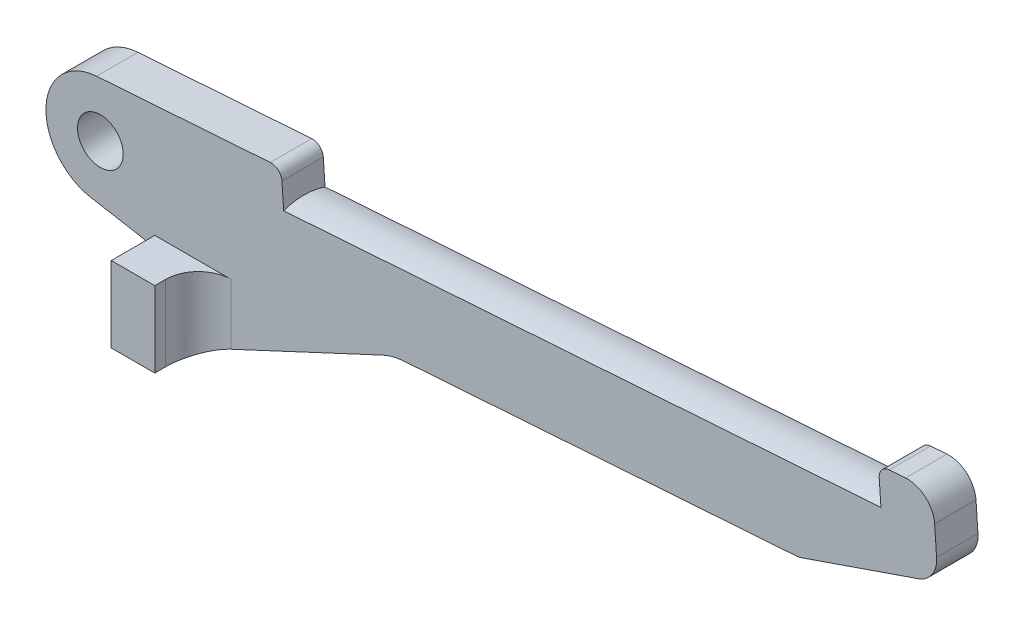
SolidWorks part; units mm, degrees
ref_plane "Front Plane" through (0, 0, 0) normal (0, 0, 1) x (1, 0, 0)
ref_plane "Top Plane" through (0, 0, 0) normal (0, 1, 0) x (1, 0, 0)
ref_plane "Right Plane" through (0, 0, 0) normal (1, 0, 0) x (0, 0, -1)
sketch "Sketch1" plane through (0, 0, 0) normal (0, 0, 1) x (1, 0, 0)
  line L0 (10, 131.0662) -> (10, -29.5109) construction
  line L1 (-1.7365, -9.8481) -> (7.5209, -11.4804)
  line L2 (10, -14.4348) -> (10, -23.9175)
  line L3 (10, -23.9175) -> (18, -23.9175)
  line L4 (18, -23.9175) -> (52.0166, -8.0553)
  line L5 (55.5452, -7.1428) -> (127.6748, -2.099)
  line L6 (88.2212, -3) -> (186.7715, -3) construction
  line L7 (184.3331, 3) -> (92.8947, 3) construction
  line L8 (153.6363, 10.5795) -> (153.2761, 15.7303)
  line L9 (-0.6976, 9.9756) -> (33.2196, 12.3474)
  line L10 (33.2196, 12.3474) -> (33.6382, 6.362)
  line L11 (33.6382, 6.362) -> (143.3702, 14.0352)
  line L12 (143.3702, 14.0352) -> (142.9517, 20.0206)
  line L13 (142.9517, 20.0206) -> (147.9395, 20.3694)
  line L14 (33.6382, 6.362) -> (25.6162, 121.0818) construction
  line L15 (25.6162, 121.0818) -> (25.2572, 121.0567) construction
  line L16 (150.2763, 5.5032) -> (128.9539, -1.8387)
  circle A0 centre (0, 0) radius 4.2
  arc A1 (-0.6976, 9.9756) -> (-1.7365, -9.8481) centre (0, 0) ccw
  arc A2 (127.6748, -2.099) -> (128.9539, -1.8387) centre (127.326, 2.8889) ccw
  arc A3 (147.9395, 20.3694) -> (153.2761, 15.7303) centre (148.2883, 15.3815) cw
  arc A4 (7.5209, -11.4804) -> (10, -14.4348) centre (7, -14.4348) cw
  arc A5 (52.0166, -8.0553) -> (55.5452, -7.1428) centre (56.2428, -17.1184) cw
  arc A6 (153.6363, 10.5795) -> (150.2763, 5.5032) centre (148.6484, 10.2307) cw
  point P24 (152.9273, 20.7181)
  point P32 (10, -11.9175)
  point P36 (153.9039, 6.7522)
  dimension "D1" = 8.4
  dimension "D3" = 20
  dimension "D17" = 8
  dimension "D18" = 15
  dimension "D19" = 3
  dimension "D20" = 10
  dimension "D21" = 5
  dimension "D13" = 5
  dimension "D2" = 10
  dimension "D4" = 280
  dimension "D5" = 8
  dimension "D6" = 12
  dimension "D7" = 86
  dimension "D8" = 34
  dimension "D9" = 6
  dimension "D10" = 110
  dimension "D11" = 10
  dimension "D12" = 15
  dimension "D14" = 25
  dimension "D15" = 6
  dimension "D16" = 115
extrude "Boss-Extrude1" add sketch "Sketch1" along normal blind 7.6
sketch "Sketch2" plane through (0, 0, 7.6) normal (0, 0, 1) x (1, 0, 0)
  line L1 (10, -23.9175) -> (18, -23.9175)
  line L2 (10, -23.9175) -> (10, -10)
  line L3 (10, -10) -> (18, -10)
  line L4 (18, -23.9175) -> (18, -10)
  dimension "D1" = 10
extrude "Boss-Extrude2" add sketch "Sketch2" along normal blind 8
fillet "Fillet1" radius 6 1 edges at (18, -16.9588, 7.6)
sketch "Sketch6" plane through (22.5121, 165.472, 0) normal (-0.9976, -0.0698, 0) x (0, 0, -1)
  line L1 (-7.6, 159.4986) -> (-7.6, 153.4986) construction
  line L2 (-7.6, 153.4986) -> (0, 153.4986) construction
  line L3 (0, 159.4986) -> (0, 153.4986) construction
  line L4 (-7.6, 160.1161) -> (-7.6, 153.4986)
  line L5 (-7.6, 153.4986) -> (0, 153.4986)
  line L10 (0, 160.1161) -> (0, 153.4986)
  line L11 (-7.6, 173.2015) -> (-7.6, 153.4986) construction
  line L12 (0, 153.4986) -> (0, 173.2015) construction
  line L13 (-7.6, 159.4986) -> (0, 159.4986) construction
  arc A0 (-7.6, 160.1161) -> (0, 160.1161) centre (-3.8, 171.4986) ccw
  dimension "D1" = 12
extrude "Cut-Extrude2" cut sketch "Sketch6" against normal up to surface (110 mm away) up to face at (143.1609, 17.0279, 3.8)
fillet "Fillet2" radius 2 2 edges at (142.9517, 20.0206, 3.8) (33.2196, 12.3474, 3.8)
